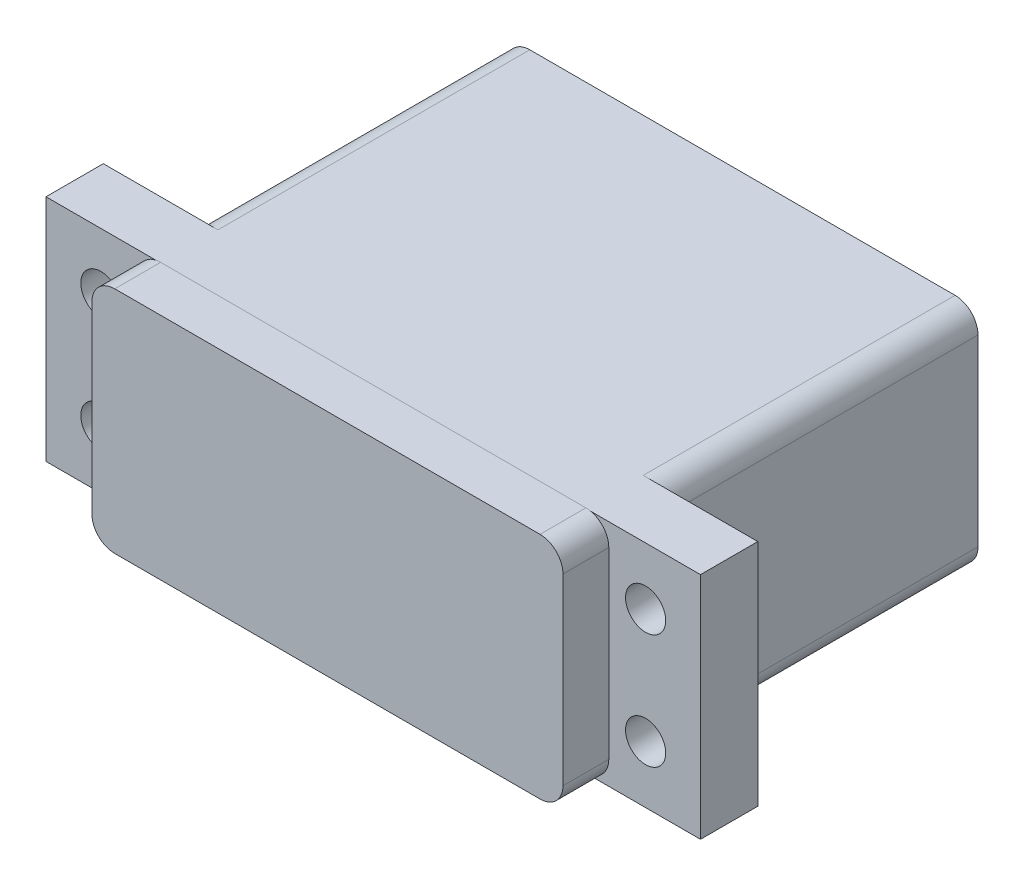
SolidWorks part; units mm, degrees
ref_plane "Front Plane" through (0, 0, 0) normal (0, 0, 1) x (1, 0, 0)
ref_plane "Top Plane" through (0, 0, 0) normal (0, 1, 0) x (1, 0, 0)
ref_plane "Right Plane" through (0, 0, 0) normal (1, 0, 0) x (0, 0, -1)
sketch "Sketch1" plane through (0, 0, 0) normal (0, 0, 1) x (1, 0, 0)
  line L1 (9.9463, -5.3246) -> (47.0463, -5.3246)
  line L2 (7.9463, -7.3246) -> (7.9463, -23.3246)
  line L3 (9.9463, -25.3246) -> (47.0463, -25.3246)
  line L4 (49.0463, -7.3246) -> (49.0463, -23.3246)
  arc A0 (47.0463, -25.3246) -> (49.0463, -23.3246) centre (47.0463, -23.3246) ccw
  arc A1 (7.9463, -23.3246) -> (9.9463, -25.3246) centre (9.9463, -23.3246) ccw
  arc A2 (7.9463, -7.3246) -> (9.9463, -5.3246) centre (9.9463, -7.3246) cw
  arc A3 (47.0463, -5.3246) -> (49.0463, -7.3246) centre (47.0463, -7.3246) cw
  point P6 (49.0463, -25.3246)
  point P11 (7.9463, -5.3246)
  point P14 (49.0463, -5.3246)
  dimension "D3" = 2
  dimension "D1" = 20
  dimension "D2" = 41.1
extrude "Boss-Extrude1" add sketch "Sketch1" along normal blind 27.21
sketch "Sketch2" plane through (0, 0, 27.21) normal (0, 0, 1) x (1, 0, 0)
  line L0 (49.0463, -23.3246) -> (49.0463, -7.3246) construction
  line L1 (-0.0537, -5.3246) -> (57.0463, -5.3246)
  line L2 (-0.0537, -5.3246) -> (-0.0537, -25.3246)
  line L3 (-0.0537, -25.3246) -> (57.0463, -25.3246)
  line L4 (57.0463, -5.3246) -> (57.0463, -25.3246)
  line L5 (7.9463, -7.3246) -> (7.9463, -23.3246) construction
  line L6 (28.4963, -5.3246) -> (-0.0537, -5.3246) construction
  line L7 (47.0463, -5.3246) -> (9.9463, -5.3246) construction
  line L8 (28.4963, -25.3246) -> (57.0463, -25.3246) construction
  line L9 (9.9463, -25.3246) -> (47.0463, -25.3246) construction
  point P10 (28.4963, -5.3246)
  dimension "D1" = 8
  dimension "D2" = 8
extrude "Boss-Extrude2" add sketch "Sketch2" along normal blind 5
sketch "Sketch3" plane through (0, 0, 32.21) normal (0, 0, 1) x (1, 0, 0)
  line L0 (9.9463, -5.2793) -> (47.0463, -5.2793)
  line L1 (7.9463, -7.2793) -> (7.9463, -23.2793)
  line L2 (9.9463, -25.2793) -> (47.0463, -25.2793)
  line L3 (49.0463, -7.2793) -> (49.0463, -23.2793)
  line L5 (-0.0537, -5.3246) -> (-0.0537, -25.3246) construction
  line L6 (57.0463, -25.3246) -> (57.0463, -5.3246) construction
  arc A0 (47.0463, -25.2793) -> (49.0463, -23.2793) centre (47.0463, -23.2793) ccw
  arc A1 (7.9463, -23.2793) -> (9.9463, -25.2793) centre (9.9463, -23.2793) ccw
  arc A2 (7.9463, -7.2793) -> (9.9463, -5.2793) centre (9.9463, -7.2793) cw
  arc A3 (47.0463, -5.2793) -> (49.0463, -7.2793) centre (47.0463, -7.2793) cw
  dimension "D1" = 8
  dimension "D2" = 8
extrude "Boss-Extrude3" add sketch "Sketch3" along normal blind 4
sketch "Sketch4" plane through (0, 0, 32.21) normal (0, 0, 1) x (1, 0, 0)
  line L0 (4.7348, -5.3246) -> (4.7348, -25.3246) construction
  line L1 (9.5232, -5.3246) -> (-0.0537, -5.3246) construction
  line L2 (-0.0537, -25.3246) -> (57.0463, -25.3246) construction
  line L3 (-0.0537, -15.3246) -> (57.0463, -15.3246) construction
  line L4 (-0.0537, -5.3246) -> (-0.0537, -25.3246) construction
  line L5 (57.0463, -25.3246) -> (57.0463, -5.3246) construction
  line L6 (28.4963, -5.2793) -> (28.4963, -25.2793) construction
  line L7 (47.0463, -5.2793) -> (9.9463, -5.2793) construction
  line L8 (9.9463, -25.2793) -> (47.0463, -25.2793) construction
  circle A0 centre (4.7348, -10.3246) radius 1.7526
  circle A1 centre (4.7348, -20.3246) radius 1.7526
  circle A2 centre (52.2579, -20.3246) radius 1.7526
  circle A3 centre (52.2579, -10.3246) radius 1.7526
  dimension "D1" = 3.5052
  dimension "D2" = 5
extrude "Cut-Extrude1" cut sketch "Sketch4" against normal blind 5.63
